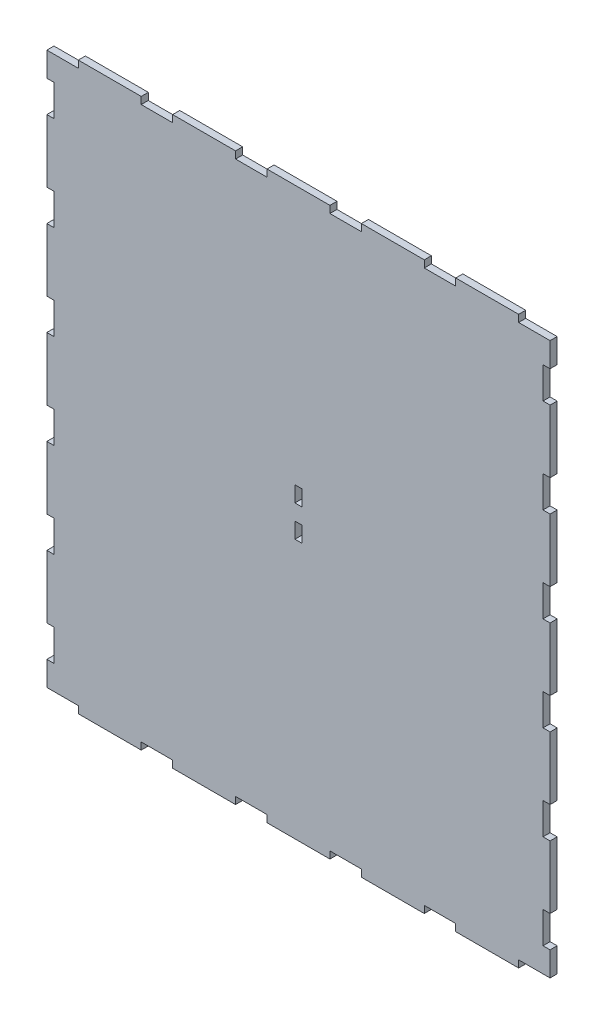
SolidWorks part; units mm, degrees
ref_plane "Front Plane" through (0, 0, 0) normal (0, 0, 1) x (1, 0, 0)
ref_plane "Top Plane" through (0, 0, 0) normal (0, 1, 0) x (1, 0, 0)
ref_plane "Right Plane" through (0, 0, 0) normal (1, 0, 0) x (0, 0, -1)
sketch "Sketch1" plane through (0, 0, 0) normal (0, 0, 1) x (1, 0, 0)
  line L1 (-203.2, -228.6) -> (203.2, -228.6)
  line L2 (-203.2, -228.6) -> (-203.2, 228.6)
  line L3 (-203.2, 228.6) -> (203.2, 228.6)
  line L4 (203.2, -228.6) -> (203.2, 228.6)
  line L5 (-203.2, -228.6) -> (203.2, 228.6) construction
  line L6 (-203.2, 228.6) -> (203.2, -228.6) construction
  point P0 (0, 0)
  dimension "D1" = 406.4
  dimension "D2" = 457.2
extrude "Boss-Extrude1" add sketch "Sketch1" along normal blind 5.715
sketch "Sketch2" plane through (0, 0, 0) normal (0, 0, 1) x (1, 0, 0)
  line L0 (203.2, -228.6) -> (203.2, 228.6) construction
  line L1 (-203.2, 228.6) -> (203.2, 228.6)
  line L2 (-203.2, 228.6) -> (-203.2, 107.442)
  line L3 (-203.2, 107.442) -> (203.2, 107.442)
  line L4 (203.2, 228.6) -> (203.2, 107.442)
  dimension "D1" = 121.158
extrude "Cut-Extrude1" [suppressed] cut sketch "Sketch2" against normal through all and the other way through all
sketch "Sketch3" plane through (0, 0, 0) normal (0, 0, -1) x (-1, 0, 0)
  line L0 (-63.5, -152.4) -> (63.5, -152.4) construction
  line L1 (0, -152.4) -> (0, 0) construction
  line L2 (-63.5, -180.975) -> (-63.5, -188.849) construction
  line L3 (63.5, -180.975) -> (63.5, -188.849) construction
  line L5 (-70.485, -186.055) -> (-56.515, -186.055)
  line L6 (-70.485, -186.055) -> (-70.485, -191.643)
  line L7 (-70.485, -191.643) -> (-56.515, -191.643)
  line L8 (-56.515, -186.055) -> (-56.515, -191.643)
  line L9 (-70.485, -186.055) -> (-56.515, -191.643) construction
  line L10 (-70.485, -191.643) -> (-56.515, -186.055) construction
  line L11 (56.515, -186.055) -> (70.485, -186.055)
  line L12 (56.515, -186.055) -> (56.515, -191.643)
  line L13 (56.515, -191.643) -> (70.485, -191.643)
  line L14 (70.485, -186.055) -> (70.485, -191.643)
  line L15 (56.515, -186.055) -> (70.485, -191.643) construction
  line L16 (56.515, -191.643) -> (70.485, -186.055) construction
  circle A0 centre (-63.5, -152.4) radius 28.575
  circle A1 centre (63.5, -152.4) radius 28.575
  dimension "D3" = 57.15
  dimension "D1" = 152.4
  dimension "D2" = 127
  dimension "D4" = 5.08
  dimension "D5" = 13.97
  dimension "D6" = 5.588
extrude "IR Sensor Cuts" [suppressed] cut sketch "Sketch3" against normal through all both and the other way through all contours A0
sketch "Sketch6" [suppressed] plane through (0, 0, 0) normal (0, 0, -1) x (-1, 0, 0)
  line L0 (-34.925, -152.4) -> (0, -152.4) construction
  line L1 (0, -152.4) -> (34.925, -152.4) construction
  circle A0 centre (0, -152.4) radius 12.7
  circle A1 centre (-63.5, -152.4) radius 28.575 construction
  circle A2 centre (63.5, -152.4) radius 28.575 construction
  dimension "D1" = 25.4
extrude "Cut-Extrude2" [suppressed] cut sketch "Sketch6" against normal through all
sketch "Sketch4" plane through (0, 0, 0) normal (0, 0, -1) x (-1, 0, 0)
  line L0 (-127, -228.6) -> (-101.6, -228.6)
  line L1 (-203.2, -228.6) -> (-177.8, -228.6)
  line L2 (-203.2, -228.6) -> (-203.2, -222.885)
  line L3 (-203.2, -222.885) -> (-177.8, -222.885)
  line L4 (-177.8, -228.6) -> (-177.8, -222.885)
  line L5 (-127, -228.6) -> (-127, -222.885)
  line L6 (-127, -222.885) -> (-101.6, -222.885)
  line L7 (-101.6, -228.6) -> (-101.6, -222.885)
  line L8 (-50.8, -228.6) -> (-25.4, -228.6)
  line L9 (-50.8, -228.6) -> (-50.8, -222.885)
  line L10 (-50.8, -222.885) -> (-25.4, -222.885)
  line L11 (-25.4, -228.6) -> (-25.4, -222.885)
  line L12 (25.4, -228.6) -> (50.8, -228.6)
  line L13 (25.4, -228.6) -> (25.4, -222.885)
  line L14 (25.4, -222.885) -> (50.8, -222.885)
  line L15 (50.8, -228.6) -> (50.8, -222.885)
  line L16 (101.6, -228.6) -> (127, -228.6)
  line L17 (101.6, -228.6) -> (101.6, -222.885)
  line L18 (101.6, -222.885) -> (127, -222.885)
  line L19 (127, -228.6) -> (127, -222.885)
  line L20 (177.8, -228.6) -> (203.2, -228.6)
  line L21 (177.8, -228.6) -> (177.8, -222.885)
  line L22 (177.8, -222.885) -> (203.2, -222.885)
  line L23 (203.2, -228.6) -> (203.2, -222.885)
  line L24 (203.2, -228.6) -> (-203.2, -228.6) construction
  dimension "D1" = 25.4
  dimension "D3" = 5.715
  dimension "D4" = 50.8
  dimension "D2" = 6
extrude "Front Jigsaw" cut sketch "Sketch4" against normal through all
mirror "Back Jigsaw" about plane through (0, 0, 0) normal (0, 1, 0) of "Front Jigsaw"
sketch "Sketch5" plane through (0, 0, 0) normal (0, 0, -1) x (-1, 0, 0)
  line L0 (203.2, 222.885) -> (203.2, -222.885) construction
  line L1 (203.2, 203.2) -> (197.485, 203.2)
  line L2 (203.2, 203.2) -> (203.2, 177.8)
  line L3 (203.2, 177.8) -> (197.485, 177.8)
  line L4 (197.485, 203.2) -> (197.485, 177.8)
  line L6 (127, 228.6) -> (177.8, 228.6) construction
  line L7 (203.2, 127) -> (197.485, 127)
  line L8 (203.2, 127) -> (203.2, 101.6)
  line L9 (203.2, 101.6) -> (197.485, 101.6)
  line L10 (197.485, 127) -> (197.485, 101.6)
  line L11 (203.2, 50.8) -> (197.485, 50.8)
  line L12 (203.2, 50.8) -> (203.2, 25.4)
  line L13 (203.2, 25.4) -> (197.485, 25.4)
  line L14 (197.485, 50.8) -> (197.485, 25.4)
  line L15 (203.2, -25.4) -> (197.485, -25.4)
  line L16 (203.2, -25.4) -> (203.2, -50.8)
  line L17 (203.2, -50.8) -> (197.485, -50.8)
  line L18 (197.485, -25.4) -> (197.485, -50.8)
  line L19 (203.2, -101.6) -> (197.485, -101.6)
  line L20 (203.2, -101.6) -> (203.2, -127)
  line L21 (203.2, -127) -> (197.485, -127)
  line L22 (197.485, -101.6) -> (197.485, -127)
  line L23 (203.2, -177.8) -> (197.485, -177.8)
  line L24 (203.2, -177.8) -> (203.2, -203.2)
  line L25 (203.2, -203.2) -> (197.485, -203.2)
  line L26 (197.485, -177.8) -> (197.485, -203.2)
  dimension "D1" = 5.715
  dimension "D2" = 25.4
  dimension "D3" = 25.4
  dimension "D5" = 50.8
  dimension "D4" = 6
extrude "Right Jigsaw" cut sketch "Sketch5" against normal through all
mirror "Left Jigsaw" about plane through (0, 0, 0) normal (1, 0, 0) of "Right Jigsaw"
other "Kerf Left Hand Hole" [suppressed] parameters "D1"=0.254
other "Kerf RIght Hand Hole" [suppressed] parameters "D1"=0.254
sketch "Sketch7" plane through (0, 0, 0) normal (0, 0, -1) x (-1, 0, 0)
  line L0 (0, 6.35) -> (0, -6.35) construction
  line L1 (-2.8575, 19.05) -> (2.8575, 19.05)
  line L2 (-2.8575, 19.05) -> (-2.8575, 6.35)
  line L3 (-2.8575, 6.35) -> (2.8575, 6.35)
  line L4 (2.8575, 19.05) -> (2.8575, 6.35)
  line L5 (-2.8575, -6.35) -> (2.8575, -6.35)
  line L6 (-2.8575, -6.35) -> (-2.8575, -19.05)
  line L7 (-2.8575, -19.05) -> (2.8575, -19.05)
  line L8 (2.8575, -6.35) -> (2.8575, -19.05)
  point P10 (0, 0)
  dimension "D1" = 12.7
  dimension "D2" = 12.7
  dimension "D3" = 5.715
extrude "Center Support Jig" cut sketch "Sketch7" against normal through all
